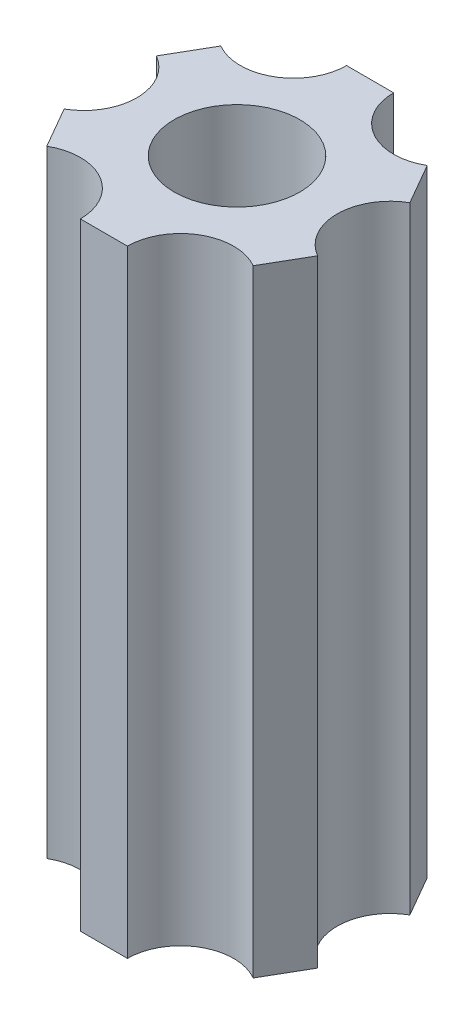
SolidWorks part; units mm, degrees
ref_plane "Front Plane" through (0, 0, 0) normal (0, 0, 1) x (1, 0, 0)
ref_plane "Top Plane" through (0, 0, 0) normal (0, 1, 0) x (1, 0, 0)
ref_plane "Right Plane" through (0, 0, 0) normal (1, 0, 0) x (0, 0, -1)
sketch "Sketch1" plane through (0, 0, 0) normal (0, 1, 0) x (1, 0, 0)
  line L1 (3.6573, -6.3551) -> (7.3323, -0.0102)
  line L2 (7.3323, -0.0102) -> (3.675, 6.3449)
  line L3 (3.675, 6.3449) -> (-3.6573, 6.3551)
  line L4 (-3.6573, 6.3551) -> (-7.3323, 0.0102)
  line L5 (-7.3323, 0.0102) -> (-3.675, -6.3449)
  line L6 (-3.675, -6.3449) -> (3.6573, -6.3551)
  circle A0 centre (0, 0) radius 6.35 construction
  circle A1 centre (-3.6573, 6.3551) radius 2.54
  circle A2 centre (3.675, 6.3449) radius 2.54
  circle A3 centre (7.3323, -0.0102) radius 2.54
  circle A4 centre (3.6573, -6.3551) radius 2.54
  circle A5 centre (-3.675, -6.3449) radius 2.54
  circle A6 centre (-7.3323, 0.0102) radius 2.54
  dimension "D2" = 5.08
  dimension "D1" = 12.7
  dimension "D3" = 6
extrude "Boss-Extrude1" add sketch "Sketch1" along normal blind 29.464 contours A6 L5 A5 L6 A4 L1 A3 L2 A2 L3 A1 L4
sketch "Sketch2" plane through (0, 29.464, 0) normal (0, 1, 0) x (1, 0, 0)
  circle A0 centre (0, 0) radius 3
  dimension "D1" = 6
extrude "Cut-Extrude1" cut sketch "Sketch2" against normal blind 254
